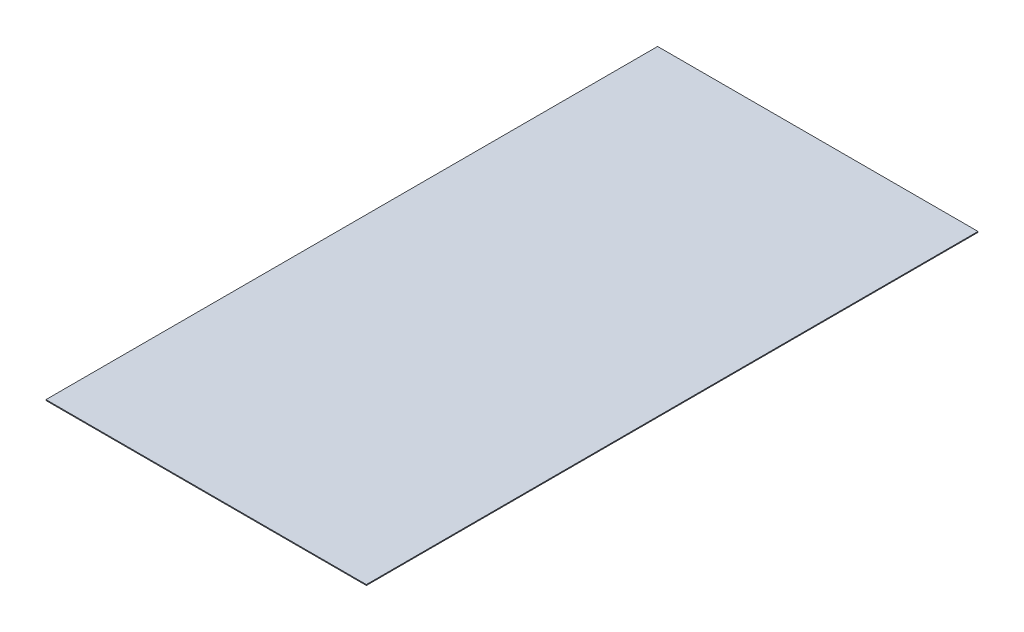
SolidWorks part; units mm, degrees
material "Glass"
ref_plane "Front Plane" through (0, 0, 0) normal (0, 0, 1) x (1, 0, 0)
ref_plane "Top Plane" through (0, 0, 0) normal (0, 1, 0) x (1, 0, 0)
ref_plane "Right Plane" through (0, 0, 0) normal (1, 0, 0) x (0, 0, -1)
sketch "Sketch1" plane through (0, 0, 0) normal (0, 1, 0) x (1, 0, 0)
  line L1 (-550, -1050) -> (550, -1050)
  line L2 (-550, -1050) -> (-550, 1050)
  line L3 (-550, 1050) -> (550, 1050)
  line L4 (550, -1050) -> (550, 1050)
  line L5 (-550, -1050) -> (550, 1050) construction
  line L6 (-550, 1050) -> (550, -1050) construction
  point P0 (0, 0)
  dimension "D1" = 1100
  dimension "D2" = 2100
extrude "Boss-Extrude1" add sketch "Sketch1" along normal blind 3
equation "\"absorber_plate_width\" = 1100mm"
equation "\"absorber_plate_length\" = 2100mm"
equation "\"absorber_plate_thickness\" = .1875in"
equation "\"groove_depth\" = 20mm"
equation "\"frame_thickness\" = 60mm"
equation "\"insulation_thickness\" = 50mm"
equation "\"glass_thickness\" = 3mm"
equation "\"D1@Boss-Extrude1\"=\"glass_thickness\""
equation "\"pipe_distances\" = 100mm"
equation "\"pipe_OD\" = 0.3125in"
equation "\"pipe_ID\" = 0.249in"
equation "\"pipe_straight_length\" = 900mm"
equation "\"absorber_to_glass\" = 25mm"
equation "\"serpentine_length\" = 1900mm"
equation "\"wood_width\" = 3.5in"
equation "\"wood_height\" = 1.5in"
